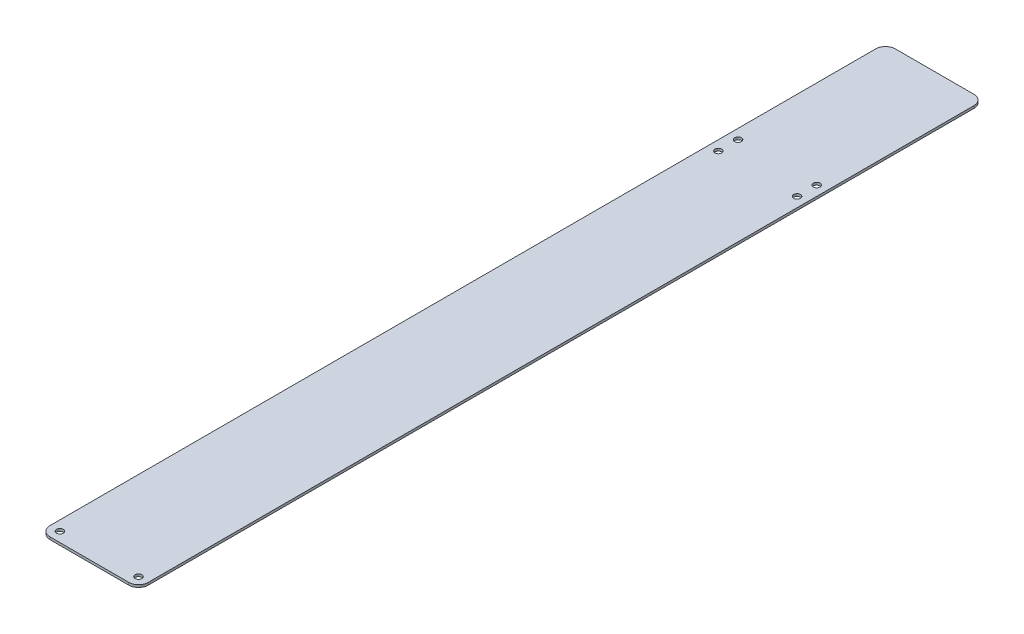
SolidWorks part; units mm, degrees
ref_plane "Front Plane" through (0, 0, 0) normal (0, 0, 1) x (1, 0, 0)
ref_plane "Top Plane" through (0, 0, 0) normal (0, 1, 0) x (1, 0, 0)
ref_plane "Right Plane" through (0, 0, 0) normal (1, 0, 0) x (0, 0, -1)
sketch "Sketch1" plane through (0, 0, 0) normal (0, 1, 0) x (1, 0, 0)
  line L1 (6.35, 0) -> (57.15, 0)
  line L2 (0, 6.35) -> (0, 539.75)
  line L3 (6.35, 546.1) -> (57.15, 546.1)
  line L4 (63.5, 6.35) -> (63.5, 539.75)
  arc A2 (6.35, 546.1) -> (0, 539.75) centre (6.35, 539.75) ccw
  arc A3 (63.5, 539.75) -> (57.15, 546.1) centre (57.15, 539.75) ccw
  circle A4 centre (6.35, 6.35) radius 2.1828
  circle A5 centre (57.15, 6.35) radius 2.1828
  arc A6 (6.35, 0) -> (0, 6.35) centre (6.35, 6.35) cw
  arc A7 (63.5, 6.35) -> (57.15, 0) centre (57.15, 6.35) cw
  circle A8 centre (6.35, 431.8) radius 2.1828
  circle A9 centre (6.35, 444.5) radius 2.1828
  circle A10 centre (57.15, 431.8) radius 2.1828
  circle A11 centre (57.15, 444.5) radius 2.1828
  point P19 (0, 0)
  dimension "D7" = 12.7
  dimension "D8" = 4.3656
  dimension "D9" = 6.35
  dimension "D10" = 6.35
  dimension "D15" = 4.3656
  dimension "D16" = 4.3656
  dimension "D17" = 6.35
  dimension "D18" = 6.35
  dimension "D4" = 431.8
  dimension "D3" = 6.35
  dimension "D5" = 4.3656
  dimension "D22" = 4.3656
  dimension "D23" = 4.3656
  dimension "D1" = 63.5
  dimension "D2" = 546.1
  dimension "D6" = 6.35
  dimension "D11" = 6.35
  dimension "D12" = 6.35
  dimension "D13" = 6.35
  dimension "D14" = 6.35
  dimension "D19" = 431.8
  dimension "D20" = 6.35
  dimension "D21" = 12.7
  dimension "D24" = 6.35
extrude "Boss-Extrude1" add sketch "Sketch1" along normal mid plane 1.5875
